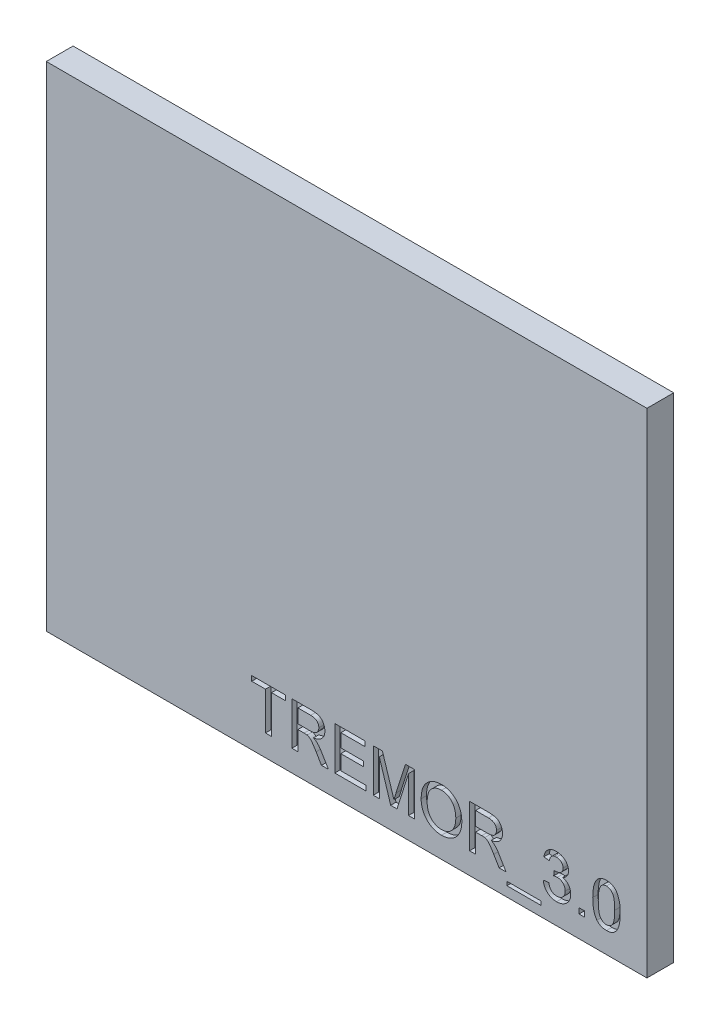
SolidWorks part; units mm, degrees
ref_plane "Спереди" through (0, 0, 0) normal (0, 0, 1) x (1, 0, 0)
ref_plane "Сверху" through (0, 0, 0) normal (0, 1, 0) x (1, 0, 0)
ref_plane "Справа" through (0, 0, 0) normal (1, 0, 0) x (0, 0, -1)
sketch "Эскиз1" plane through (0, 0, 0) normal (0, 0, 1) x (1, 0, 0)
  line L1 (-28, 23) -> (28, 23)
  line L2 (-28, 23) -> (-28, -23)
  line L3 (-28, -23) -> (28, -23)
  line L4 (28, 23) -> (28, -23)
  line L5 (-28, 23) -> (28, -23) construction
  line L6 (-28, -23) -> (28, 23) construction
  point P0 (0, 0)
extrude "Бобышка-Вытянуть2" add sketch "Эскиз1" along normal blind 2.5
sketch "Эскиз3" plane through (0, 0, 2.5) normal (0, 0, 1) x (1, 0, 0)
  text T0 "TREMOR_3.0"
  point P0 (0, 0)
  point P2 (0, 0)
  point P4 (0, 0)
  point P5 (-14, -19.8618)
extrude "Вырез-Вытянуть2" cut sketch "Эскиз3" against normal blind 0.5
